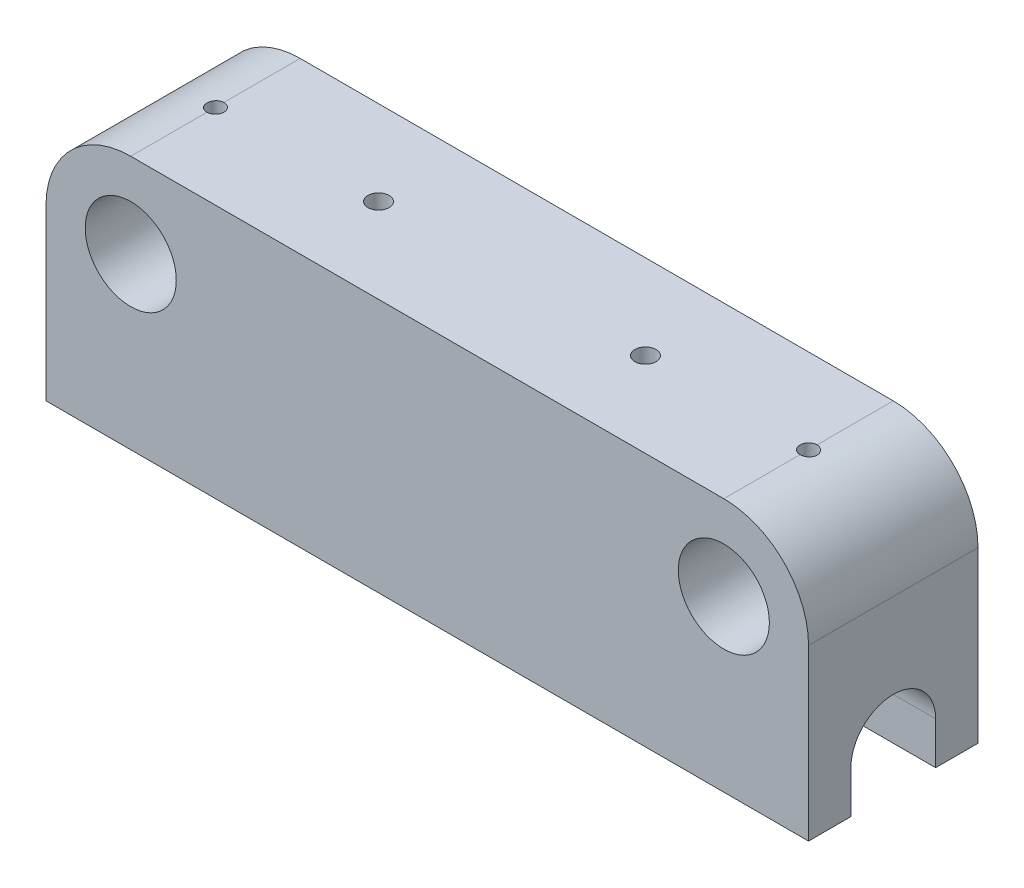
SolidWorks part; units mm, degrees
ref_plane "Front Plane" through (0, 0, 0) normal (0, 0, 1) x (1, 0, 0)
ref_plane "Top Plane" through (0, 0, 0) normal (0, 1, 0) x (1, 0, 0)
ref_plane "Right Plane" through (0, 0, 0) normal (1, 0, 0) x (0, 0, -1)
sketch "Sketch1" plane through (0, 0, 0) normal (0, 0, 1) x (1, 0, 0)
  line L4 (-70, 34.6965) -> (70, 34.6965) construction
  line L5 (-70, 54.6965) -> (70, 54.6965)
  line L6 (-90, 34.6965) -> (-90, 14.6965)
  line L7 (90, 34.6965) -> (90, 14.6965)
  line L8 (-90, 14.6965) -> (90, 14.6965)
  circle A0 centre (70, 34.6965) radius 10.75
  circle A1 centre (-70, 34.6965) radius 10.75
  arc A7 (-70, 54.6965) -> (-90, 34.6965) centre (-70, 34.6965) ccw
  arc A8 (90, 34.6965) -> (70, 54.6965) centre (70, 34.6965) ccw
  dimension "D1" = 21.5
  dimension "D2" = 20
  dimension "D3" = 140
  dimension "D4" = 180
extrude "Boss-Extrude1" add sketch "Sketch1" along normal blind 40
sketch "Sketch4" plane through (0, 0, 0) normal (1, 0, 0) x (0, 0, -1)
  line L0 (0, 14.6965) -> (0, -5.3035)
  line L1 (-40, 14.6965) -> (0, 14.6965) construction
  line L3 (-40, 14.6965) -> (-40, -5.3035)
  line L4 (-40, -5.3035) -> (-30, -5.3035)
  line L5 (-30, 4.6965) -> (-30, -5.3035)
  line L6 (-10, 4.6965) -> (-10, -5.3035)
  line L7 (-10, -5.3035) -> (0, -5.3035)
  line L11 (0, 14.6965) -> (0, 34.6965)
  line L12 (0, 34.6965) -> (-40, 34.6965)
  line L13 (-40, 34.6965) -> (-40, 14.6965)
  line L14 (-40, 14.6965) -> (0, 14.6965)
  line L18 (-40, 14.6965) -> (0, 14.6965)
  arc A0 (-10, 4.6965) -> (-30, 4.6965) centre (-20, 4.6965) ccw
  point P5 (-20, 14.6965)
  dimension "D1" = 10
  dimension "D3" = 10
  dimension "D2" = 0
extrude "Boss-Extrude2" add sketch "Sketch4" along normal up to surface and the other way up to surface contours A0 L6 L7 L0 L18 | A0 L18 L3 L4 L5 up to face at (90, 24.6965, 20) other way up to face at (-90, 24.6965, 20)
sketch "Sketch5" plane through (0, 0, 0) normal (0, 1, 0) x (1, 0, 0)
  line L0 (-31.5, -20) -> (31.5, -20) construction
  line L1 (0, 0) -> (0, -40) construction
  line L2 (70, -40) -> (-70, -40) construction
  circle A0 centre (-31.5, -20) radius 2.5
  circle A1 centre (31.5, -20) radius 2.5
  point P12 (0, -20)
  point P13 (0, -20)
  dimension "D2" = 5
  dimension "D1" = 63
extrude "Cut-Extrude1" cut sketch "Sketch5" along normal up to surface (54.6965 mm away) up to face at (0, 54.6965, 20)
sketch "Sketch8" plane through (0, 54.6965, 0) normal (0, 1, 0) x (1, 0, 0)
  line L0 (-70, -40) -> (-70, 0) construction
  line L1 (70, -40) -> (70, 0) construction
  circle A0 centre (-70, -20) radius 2
  circle A1 centre (70, -20) radius 2
  dimension "D1" = 4
extrude "Cut-Extrude3" cut sketch "Sketch8" against normal up to next
